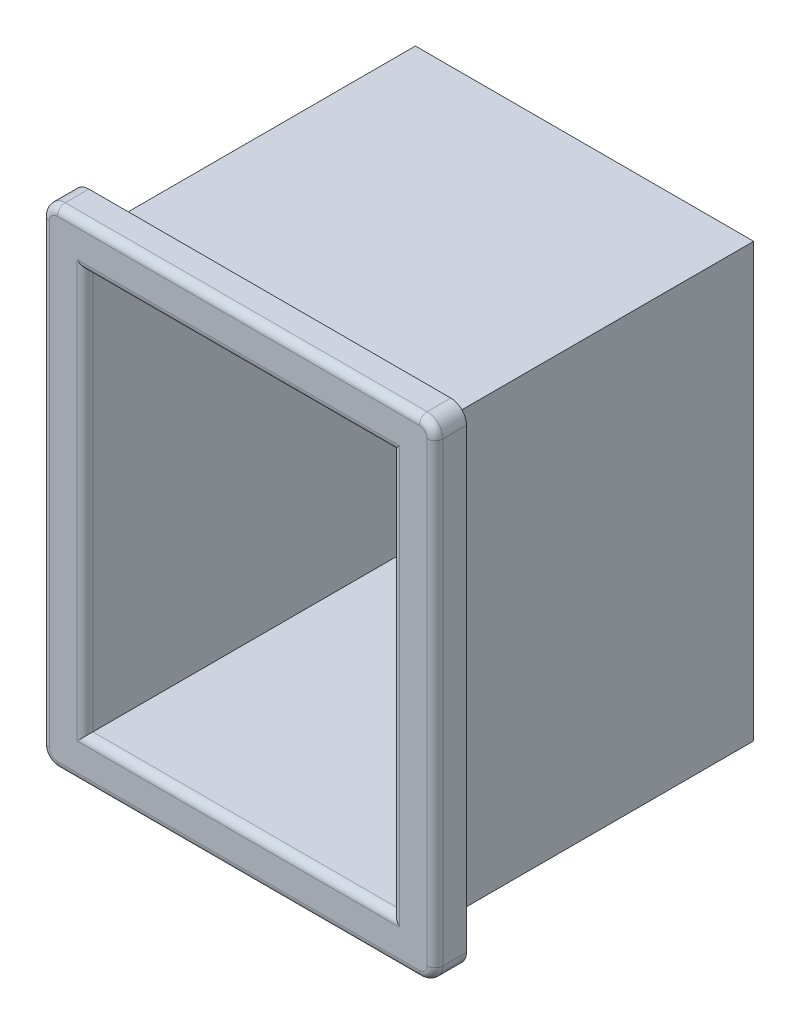
SolidWorks part; units mm, degrees
ref_plane "Front Plane" through (0, 0, 0) normal (0, 0, 1) x (1, 0, 0)
ref_plane "Top Plane" through (0, 0, 0) normal (0, 1, 0) x (1, 0, 0)
ref_plane "Right Plane" through (0, 0, 0) normal (1, 0, 0) x (0, 0, -1)
sketch "Sketch1" plane through (0, 0, 0) normal (0, 0, 1) x (1, 0, 0)
  line L1 (-10.75, 13.75) -> (10.75, 13.75)
  line L2 (-10.75, 13.75) -> (-10.75, -13.75)
  line L3 (-10.75, -13.75) -> (10.75, -13.75)
  line L4 (10.75, 13.75) -> (10.75, -13.75)
  line L5 (-10.75, 13.75) -> (10.75, -13.75) construction
  line L6 (-10.75, -13.75) -> (10.75, 13.75) construction
  point P0 (0, 0)
  dimension "D1" = 21.5
  dimension "D2" = 27.5
extrude "Boss-Extrude1" add sketch "Sketch1" along normal blind 20
sketch "Sketch2" plane through (0, 0, 20) normal (0, 0, 1) x (1, 0, 0)
  line L1 (-12.5, -15.5) -> (12.5, -15.5)
  line L2 (-12.5, -15.5) -> (-12.5, 15.5)
  line L3 (-12.5, 15.5) -> (12.5, 15.5)
  line L4 (12.5, -15.5) -> (12.5, 15.5)
  line L5 (-12.5, -15.5) -> (12.5, 15.5) construction
  line L6 (-12.5, 15.5) -> (12.5, -15.5) construction
  point P0 (0, 0)
  dimension "D1" = 25
  dimension "D2" = 31
extrude "Boss-Extrude2" add sketch "Sketch2" along normal blind 2
sketch "Sketch3" plane through (0, 0, 22) normal (0, 0, 1) x (1, 0, 0)
  line L1 (-9.75, -12.75) -> (9.75, -12.75)
  line L2 (-9.75, -12.75) -> (-9.75, 12.75)
  line L3 (-9.75, 12.75) -> (9.75, 12.75)
  line L4 (9.75, -12.75) -> (9.75, 12.75)
  line L5 (-9.75, -12.75) -> (9.75, 12.75) construction
  line L6 (-9.75, 12.75) -> (9.75, -12.75) construction
  point P0 (0, 0)
  dimension "D1" = 25.5
  dimension "D2" = 19.5
extrude "Cut-Extrude1" cut sketch "Sketch3" against normal blind 21
fillet "Fillet1" radius 1 4 edges at (-12.5, -15.5, 21) (12.5, -15.5, 21) (-12.5, 15.5, 21) (12.5, 15.5, 21)
fillet "Fillet2" radius 0.5 12 edges at (-12.2071, 15.2071, 22) (0, 15.5, 22) (12.2071, 15.2071, 22) (12.5, 0, 22) (12.2071, -15.2071, 22) (0, -15.5, 22) (-12.2071, -15.2071, 22) (-12.5, 0, 22) (-9.75, 0, 22) (0, -12.75, 22) (9.75, 0, 22) (0, 12.75, 22)
